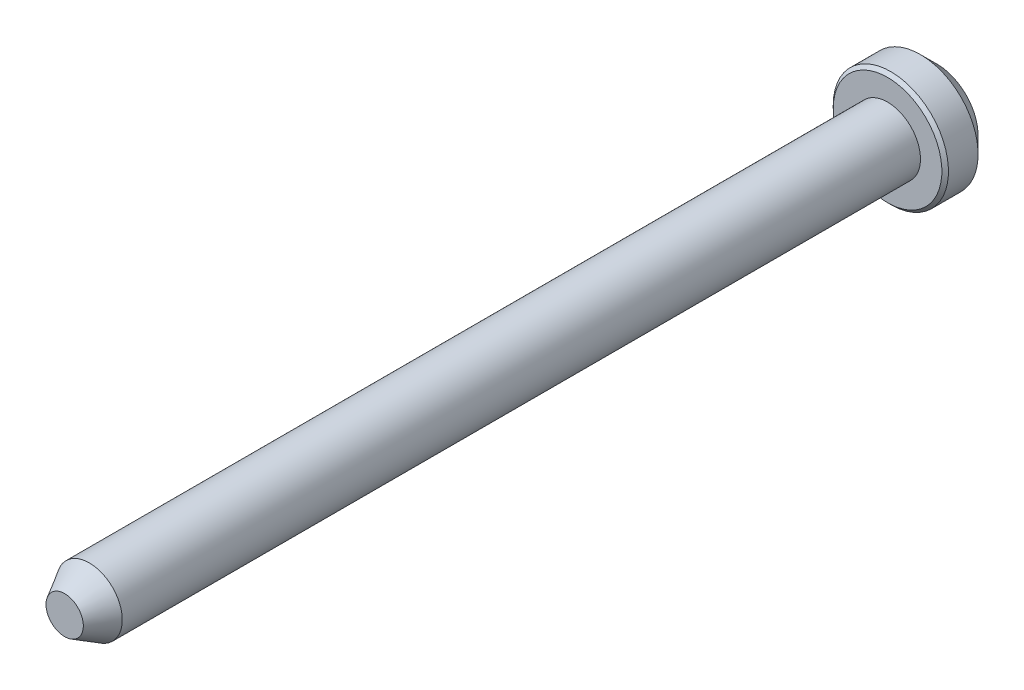
SolidWorks part; units mm, degrees
material "Plain Carbon Steel"
ref_plane "Front Plane" through (0, 0, 0) normal (0, 0, 1) x (1, 0, 0)
ref_plane "Top Plane" through (0, 0, 0) normal (0, 1, 0) x (1, 0, 0)
ref_plane "Right Plane" through (0, 0, 0) normal (1, 0, 0) x (0, 0, -1)
sketch "Sketch1" plane through (0, 0, 0) normal (0, 1, 0) x (1, 0, 0)
  line L0 (0, 0) -> (0, 53)
  line L1 (0, 53) -> (2.5, 53)
  line L2 (2.5, 53) -> (3.5, 52)
  line L3 (3.5, 52) -> (3.5, 50)
  line L4 (3.5, 50) -> (2, 50)
  line L5 (2, 50) -> (2, 1.5)
  line L6 (2, 1.5) -> (1.134, 0)
  line L7 (1.134, 0) -> (0, 0)
  line L8 (0, 0) -> (0, -10.7368) construction
  dimension "D1" = 4
  dimension "D2" = 1.5
  dimension "D3" = 60
  dimension "D4" = 3
  dimension "D5" = 50
  dimension "D6" = 7
  dimension "D7" = 45
  dimension "D8" = 1
revolve "Revolve1" add sketch "Sketch1" angle 360 about L8
chamfer "Chamfer1" distance 0.2 angle 45 1 edges at (-3.5, 0, -50)
